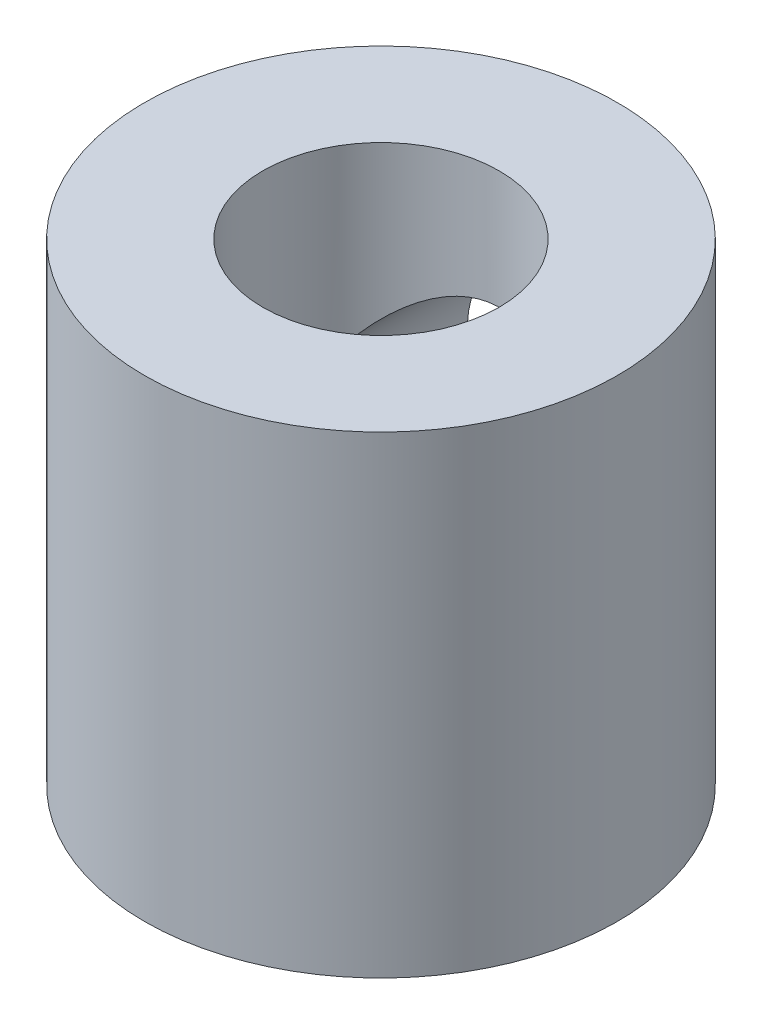
SolidWorks part; units mm, degrees
ref_plane "Front Plane" through (0, 0, 0) normal (0, 0, 1) x (1, 0, 0)
ref_plane "Top Plane" through (0, 0, 0) normal (0, 1, 0) x (1, 0, 0)
ref_plane "Right Plane" through (0, 0, 0) normal (1, 0, 0) x (0, 0, -1)
sketch "Sketch1" plane through (0, 0, 0) normal (0, 1, 0) x (1, 0, 0)
  circle A0 centre (0, 0) radius 10
  circle A1 centre (0, 0) radius 5
  dimension "D1" = 10
  dimension "D2" = 20
extrude "Boss-Extrude1" add sketch "Sketch1" along normal blind 20
sketch "Sketch2" plane through (0, 0, 0) normal (0, 0, 1) x (1, 0, 0)
  line L0 (-10, 0) -> (10, 0) construction
  circle A0 centre (0, 10) radius 5
  dimension "D1" = 10
  dimension "D2" = 10
extrude "Cut-Extrude1" cut sketch "Sketch2" against normal blind 20
